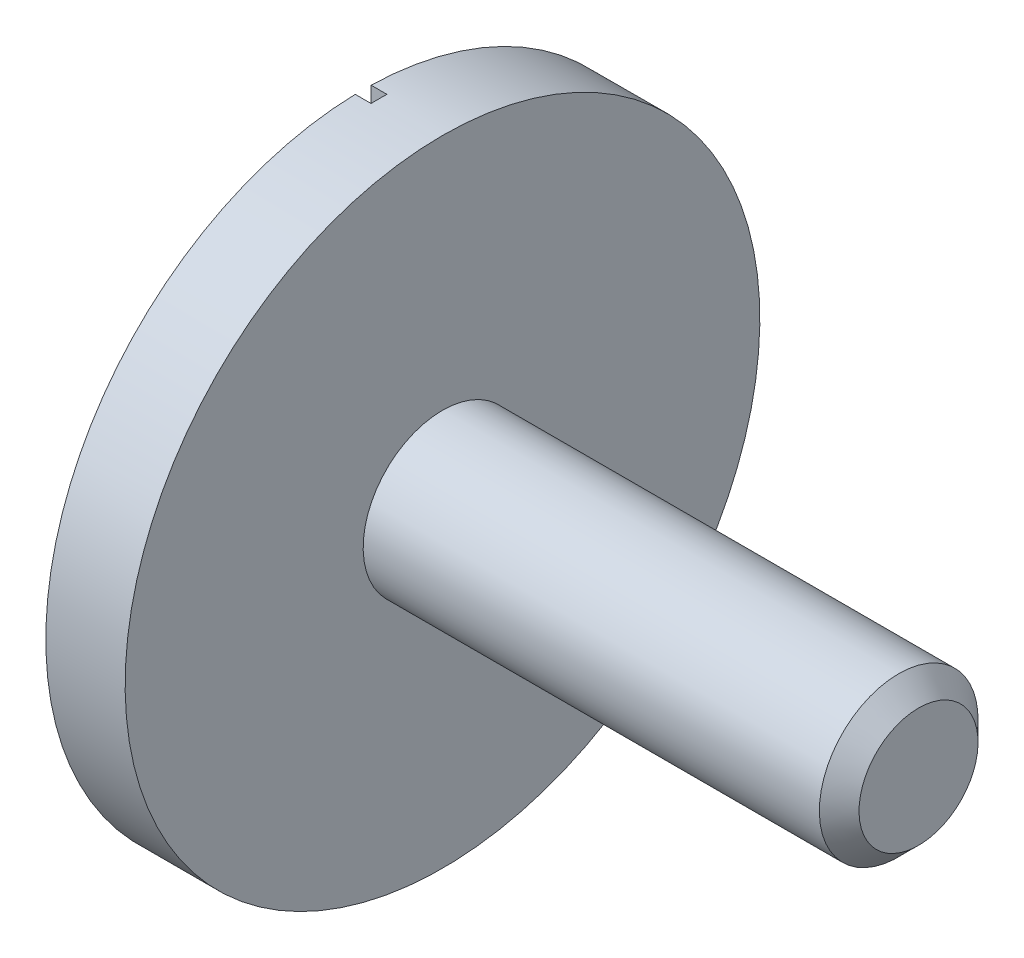
SolidWorks part; units mm, degrees
ref_plane "Front Plane" through (0, 0, 0) normal (0, 0, 1) x (1, 0, 0)
ref_plane "Top Plane" through (0, 0, 0) normal (0, 1, 0) x (1, 0, 0)
ref_plane "Right Plane" through (0, 0, 0) normal (1, 0, 0) x (0, 0, -1)
sketch "Croquis1" plane through (0, 0, 0) normal (0, 0, 1) x (1, 0, 0)
  line L0 (0, 0) -> (0, 2)
  line L1 (0, 2) -> (0.5, 2)
  line L2 (0.5, 2) -> (0.5, 0.5)
  line L3 (0.5, 0.5) -> (3.5, 0.5)
  line L4 (3.5, 0) -> (3.5, 0.5)
  line L7 (3.5, 0) -> (0, 0)
  dimension "D2" = 2
  dimension "D4" = 0.5
  dimension "D6" = 0.5
  dimension "D7" = 3.5
revolve "Revolución1" add sketch "Croquis1" angle 360 about L7
cosmetic thread "Rosca cosmética1"
chamfer "Chaflán1" distance 0.125 angle 45 1 edges at (3.5, 0.5, 0)
sketch "Croquis6" plane through (0, 0, 0) normal (-1, 0, 0) x (0, 0, 1)
  line L2 (-0.05, 1.9994) -> (-0.05, -1.9994)
  line L4 (0.05, 1.9994) -> (0.05, -1.9994)
  arc A0 (-0.05, -1.9994) -> (0.05, -1.9994) centre (0, 0) ccw
  circle A1 centre (0, 0) radius 2 construction
  arc A2 (0.05, 1.9994) -> (-0.05, 1.9994) centre (0, 0) ccw
  dimension "D1" = 0.1
extrude "Cortar-Extruir2" cut sketch "Croquis6" against normal blind 0.1
